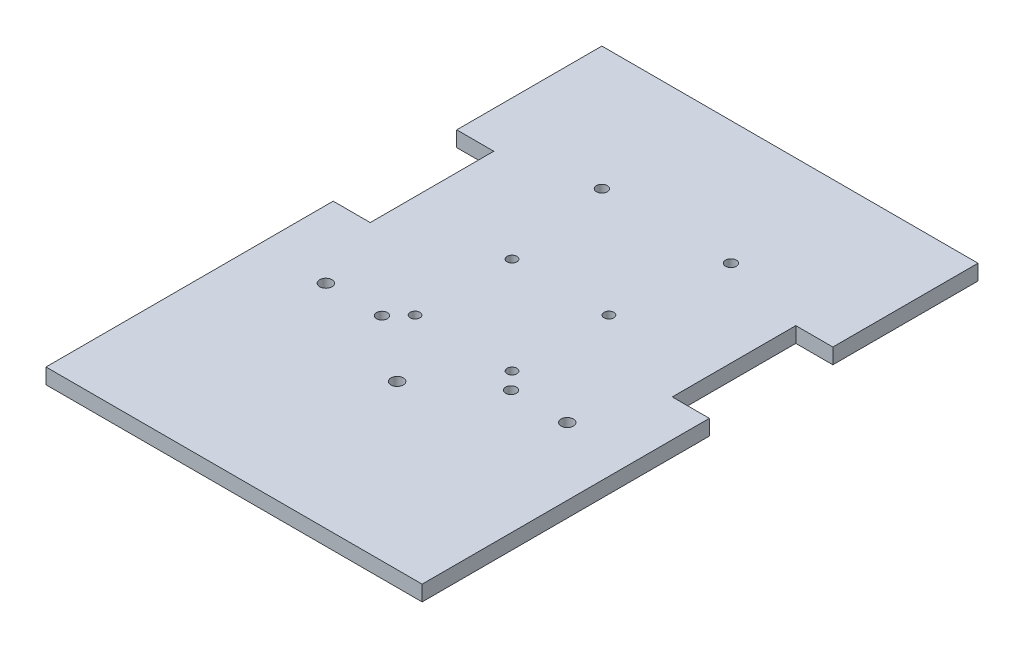
SolidWorks part; units mm, degrees
ref_plane "Front Plane" through (0, 0, 0) normal (0, 0, 1) x (1, 0, 0)
ref_plane "Top Plane" through (0, 0, 0) normal (0, 1, 0) x (1, 0, 0)
ref_plane "Right Plane" through (0, 0, 0) normal (1, 0, 0) x (0, 0, -1)
sketch "Sketch1" plane through (0, 0, 0) normal (0, 1, 0) x (1, 0, 0)
  circle A0 centre (0, 90.4441) radius 2.2225
  circle A1 centre (53.086, 90.4441) radius 2.2225
  circle A2 centre (0, 0) radius 2.2225
  circle A3 centre (53.086, 0) radius 2.2225
  dimension "D1" = 4.445
  dimension "D2" = 4.445
  dimension "D3" = 4.445
  dimension "D4" = 4.445
  dimension "D5" = 53.086
  dimension "D6" = 90.4441
  dimension "D7" = 104.8725
  dimension "D8" = 0
  dimension "D10" = 104.8725
  dimension "D11" = 53.086
  dimension "D9" = 53.086
sketch "Sketch2" plane through (0, 0, 0) normal (0, 1, 0) x (1, 0, 0)
  line L1 (-50.8, 141.2441) -> (103.886, 141.2441)
  line L2 (-50.8, 141.2441) -> (-50.8, -87.3559)
  line L3 (-50.8, -87.3559) -> (103.886, -87.3559)
  line L4 (103.886, 141.2441) -> (103.886, -87.3559)
  circle A0 centre (0, 90.4441) radius 2.2225 construction
  circle A1 centre (53.086, 90.4441) radius 2.2225 construction
  dimension "D3" = 50.8
  dimension "D1" = 50.8
  dimension "D2" = 50.8
  dimension "D4" = 228.6
extrude "Boss-Extrude1" add sketch "Sketch2" along normal blind 6.35
extrude "Cut-Extrude1" cut sketch "Sketch1" along normal blind 6.35
sketch "Sketch3" plane through (0, 6.35, 0) normal (0, 1, 0) x (1, 0, 0)
  line L0 (103.886, -87.3559) -> (103.886, 141.2441) construction
  line L1 (103.886, 81.5541) -> (88.646, 81.5541)
  line L2 (103.886, 81.5541) -> (103.886, 30.7541)
  line L3 (103.886, 30.7541) -> (88.646, 30.7541)
  line L4 (88.646, 81.5541) -> (88.646, 30.7541)
  line L5 (-50.8, 141.2441) -> (-50.8, -87.3559) construction
  line L6 (-50.8, 81.5541) -> (-35.56, 81.5541)
  line L7 (-50.8, 81.5541) -> (-50.8, 30.7541)
  line L8 (-50.8, 30.7541) -> (-35.56, 30.7541)
  line L9 (-35.56, 81.5541) -> (-35.56, 30.7541)
  circle A0 centre (0, 90.4441) radius 2.2225 construction
  point P12 (96.266, 81.5541)
  dimension "D1" = 15.24
  dimension "D2" = 15.24
  dimension "D3" = 0
  dimension "D4" = 50.8
  dimension "D5" = 50.8
  dimension "D6" = 8.89
extrude "Cut-Extrude2" cut sketch "Sketch3" against normal blind 6.35
sketch "Sketch8" plane through (0, 6.35, 0) normal (0, 1, 0) x (1, 0, 0)
  circle A0 centre (26.5501, -20.2997) radius 2.54
  circle A1 centre (-23.0771, 0.0203) radius 2.54
  circle A2 centre (76.1773, 0.0203) radius 2.54
  dimension "D1" = 5.08
  dimension "D2" = 5.08
  dimension "D3" = 5.08
  dimension "D4" = 49.6272
  dimension "D5" = 20.32
  dimension "D6" = 49.6272
  dimension "D7" = 20.32
  dimension "D9" = 26.5501
  dimension "D8" = 20.2997
extrude "Cut-Extrude3" cut sketch "Sketch8" against normal blind 17.78
sketch "Sketch10" plane through (0, 6.35, 0) normal (0, 1, 0) x (1, 0, 0)
  line L0 (6.604, 7.0051) -> (46.482, 46.8831) construction
  line L1 (-50.8, -87.3559) -> (103.886, -87.3559) construction
  line L2 (46.482, 7.0051) -> (6.604, 46.8831) construction
  line L3 (103.886, -87.3559) -> (103.886, 30.7541) construction
  circle A0 centre (6.604, 7.0051) radius 2
  circle A1 centre (46.482, 7.0051) radius 2
  circle A2 centre (46.482, 46.8831) radius 2
  circle A3 centre (6.604, 46.8831) radius 2
  circle A4 centre (26.543, 26.9441) radius 3.2512 construction
  dimension "D1" = 4
  dimension "D4" = 114.3
  dimension "D5" = 77.343
  dimension "D2" = 2
  dimension "D3" = 2
extrude "Cut-Extrude4" cut sketch "Sketch10" against normal through all
equation "\"D4@Sketch10\"=9/2"
